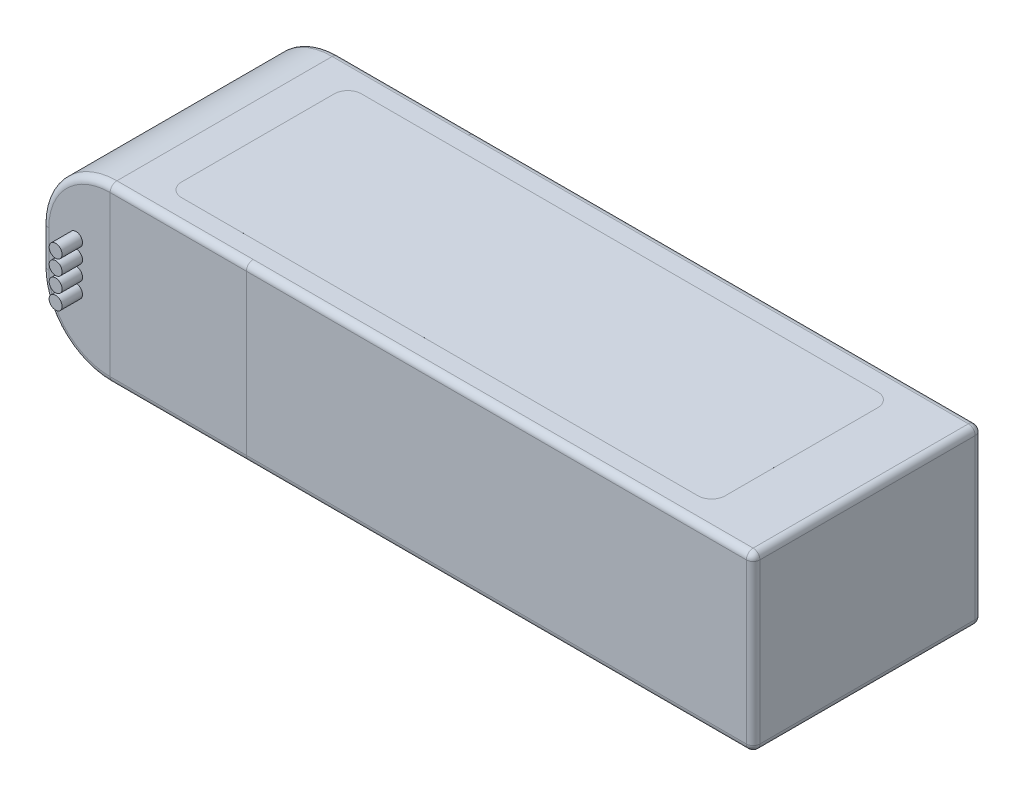
SolidWorks part; units mm, degrees
ref_plane "Plano frontal" through (0, 0, 0) normal (0, 0, 1) x (1, 0, 0)
ref_plane "Plano superior" through (0, 0, 0) normal (0, 1, 0) x (1, 0, 0)
ref_plane "Plano direito" through (0, 0, 0) normal (1, 0, 0) x (0, 0, -1)
sketch "Sketch1" plane through (0, 0, 0) normal (0, 1, 0) x (1, 0, 0)
  line L1 (-52.2, 16.8) -> (52.2, 16.8)
  line L2 (-52.2, 16.8) -> (-52.2, -16.8)
  line L3 (-52.2, -16.8) -> (52.2, -16.8)
  line L4 (52.2, 16.8) -> (52.2, -16.8)
  point P4 (0, 16.8)
  point P6 (-52.2, 0)
  dimension "D1" = 33.6
  dimension "D2" = 104.4
extrude "Boss-Extrude1" add sketch "Sketch1" along normal mid plane 25.4
fillet "Fillet1" radius 10 2 edges at (-52.2, -12.7, 0) (-52.2, 12.7, 0)
sketch "Sketch2" plane through (0, 0, -16.8) normal (0, 0, -1) x (-1, 0, 0)
  line L1 (44.2, 1.45) -> (44.2, -1.45) construction
  line L2 (52.2, 2.7) -> (52.2, -2.7) construction
  circle A0 centre (44.2, 3.35) radius 1.9
  circle A1 centre (44.2, -3.35) radius 1.9
  point P4 (44.2, 0)
  dimension "D1" = 3.8
  dimension "D2" = 2.9
  dimension "D3" = 8
extrude "Boss-Extrude2" add sketch "Sketch2" along normal blind 5
sketch "Sketch4" plane through (0, 0, 16.8) normal (0, 0, 1) x (1, 0, 0)
  line L0 (-47.2, 4.25) -> (-47.2, -4.25) construction
  line L1 (-52.2, 2.7) -> (-52.2, -2.7) construction
  circle A0 centre (-47.2, 3.3) radius 0.95
  circle A1 centre (-47.2, 1.1) radius 0.95
  circle A2 centre (-47.2, -1.1) radius 0.95
  circle A3 centre (-47.2, -3.3) radius 0.95
  point P2 (-47.2, 0)
  dimension "D1" = 1.9
  dimension "D3" = 5
  dimension "D4" = 0.3
  dimension "D2" = 4
extrude "Boss-Extrude3" add sketch "Sketch4" along normal blind 3
sketch "Sketch5" plane through (0, 0, 16.8) normal (0, 0, 1) x (1, 0, 0)
  line L0 (-42.2, -12.7) -> (52.2, -12.7) construction
  line L1 (-42.2, 12.7) -> (-22.2, 12.7)
  line L2 (-42.2, 12.7) -> (-42.2, -12.7)
  line L3 (-42.2, -12.7) -> (-22.2, -12.7)
  line L4 (-22.2, 12.7) -> (-22.2, -12.7)
  dimension "D1" = 20
extrude "Boss-Extrude4" add sketch "Sketch5" along normal blind 0.0001
mirror "Mirror1" about plane through (0, 0, 0) normal (0, 0, 1) of "Boss-Extrude4" second plane through (0, 0, 0) second plane normal (0, 1, 0)
sketch "Sketch6" plane through (0, 12.7, 0) normal (0, 1, 0) x (1, 0, 0)
  line L0 (52.2, -16.8) -> (52.2, 16.8) construction
  line L1 (-35.3, 13.2) -> (40.5, 13.2)
  line L2 (-37.3, 11.2) -> (-37.3, -11.2)
  line L3 (-35.3, -13.2) -> (40.5, -13.2)
  line L4 (42.5, 11.2) -> (42.5, -11.2)
  arc A0 (40.5, 13.2) -> (42.5, 11.2) centre (40.5, 11.2) cw
  arc A1 (40.5, -13.2) -> (42.5, -11.2) centre (40.5, -11.2) ccw
  arc A2 (-37.3, -11.2) -> (-35.3, -13.2) centre (-35.3, -11.2) ccw
  arc A3 (-35.3, 13.2) -> (-37.3, 11.2) centre (-35.3, 11.2) ccw
  point P4 (-37.3, 0)
  point P10 (42.5, 13.2)
  point P15 (-37.3, -13.2)
  point P18 (-37.3, 13.2)
  dimension "D4" = 2
  dimension "D1" = 79.8
  dimension "D2" = 26.4
  dimension "D3" = 9.7
extrude "Boss-Extrude5" add sketch "Sketch6" along normal blind 0.0001
sketch "Sketch7" plane through (0, -12.7, 0) normal (0, -1, 0) x (1, 0, 0)
  line L0 (52.2, 16.8) -> (52.2, -16.8) construction
  line L1 (-23.4, 12.5) -> (27.5, 12.5)
  line L2 (-25.4, 10.5) -> (-25.4, -10.5)
  line L3 (-23.4, -12.5) -> (27.5, -12.5)
  line L4 (29.5, 10.5) -> (29.5, -10.5)
  arc A0 (27.5, -12.5) -> (29.5, -10.5) centre (27.5, -10.5) ccw
  arc A1 (27.5, 12.5) -> (29.5, 10.5) centre (27.5, 10.5) cw
  arc A2 (-25.4, -10.5) -> (-23.4, -12.5) centre (-23.4, -10.5) ccw
  arc A3 (-23.4, 12.5) -> (-25.4, 10.5) centre (-23.4, 10.5) ccw
  point P12 (-25.4, 0)
  dimension "D1" = 2
  dimension "D2" = 54.9
  dimension "D3" = 25
  dimension "D4" = 22.7
extrude "Boss-Extrude6" add sketch "Sketch7" along normal blind 0.0001
fillet "Fillet7" radius 1 14 edges at (-49.2711, 9.7711, 16.8) (-52.2, 0, 16.8) (-49.2711, 9.7711, -16.8) (-52.2, 0, -16.8) (52.2, 0, 16.8) (52.2, 12.7, 0) (52.2, 0, -16.8) (52.2, -12.7, 0) (15, 12.7, -16.8) (15, -12.7, -16.8) (15, 12.7, 16.8) (15, -12.7, 16.8) (-49.2711, -9.7711, 16.8) (-49.2711, -9.7711, -16.8)
fillet "Fillet8" radius 1 12 edges at (-42.2, 12.7, 16.3) (-42.2, -12.7, 16.3) (-22.2, -12.7, 16.3) (-22.2, 12.7, 16.3) (-32.2, -12.7, 16.8001) (-32.2, 12.7, 16.8001) (-42.2, -12.7, -16.3) (-32.2, 12.7, -16.8001) (-42.2, 12.7, -16.3) (-22.2, 12.7, -16.3) (-32.2, -12.7, -16.8001) (-22.2, -12.7, -16.3)
